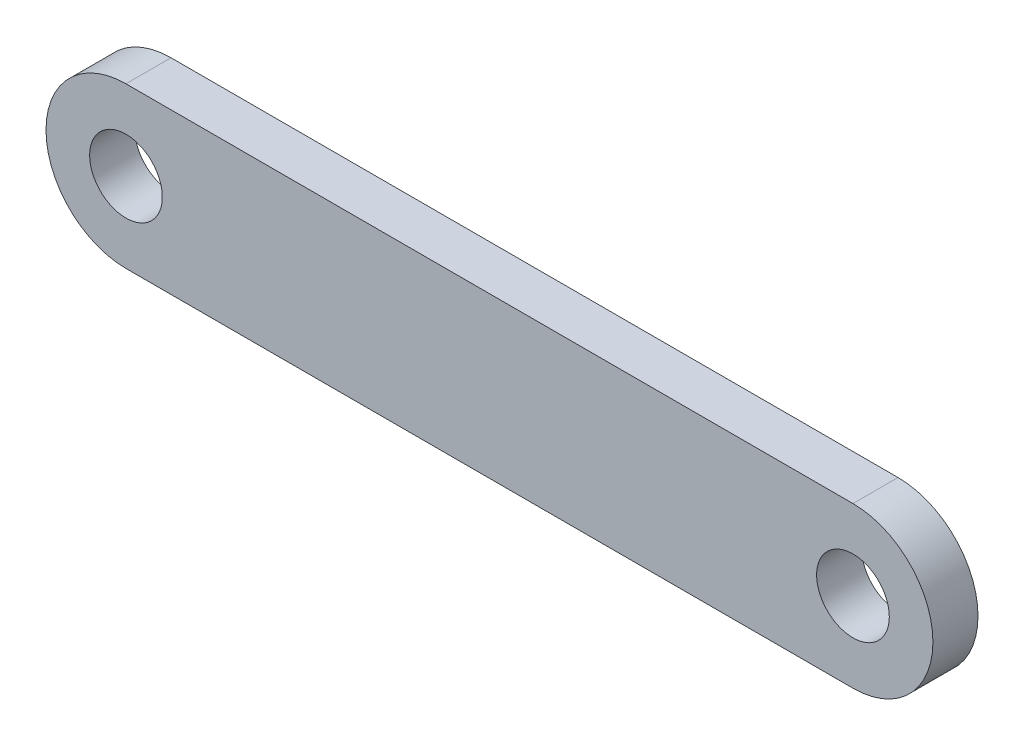
SolidWorks part; units mm, degrees
material "Teak"
ref_plane "Front Plane" through (0, 0, 0) normal (0, 0, 1) x (1, 0, 0)
ref_plane "Top Plane" through (0, 0, 0) normal (0, 1, 0) x (1, 0, 0)
ref_plane "Right Plane" through (0, 0, 0) normal (1, 0, 0) x (0, 0, -1)
sketch "Sketch1" plane through (0, 0, 0) normal (0, 0, 1) x (1, 0, 0)
  line L1 (0, 0) -> (0, 26.388) construction
  line L2 (-25, 5.0272) -> (25, 5.0272)
  line L3 (-25, -5.9728) -> (25, -5.9728)
  circle A0 centre (25, -0.4728) radius 2.5
  arc A1 (25, 5.0272) -> (25, -5.9728) centre (25, -0.4728) cw
  arc A2 (-25, 5.0272) -> (-25, -5.9728) centre (-25, -0.4728) ccw
  circle A3 centre (-25, -0.4728) radius 2.5
  point P8 (0, 5.0272)
  point P15 (0, -5.9728)
  dimension "D1" = 5
  dimension "D3" = 5.5
  dimension "D2" = 11
  dimension "D4" = 50
extrude "Boss-Extrude1" add sketch "Sketch1" along normal blind 3.1
equation "\"p\"= 20mm"
equation "\"m\"= 1"
equation "\"hole_diam\"= 4mm"
equation "\"len_grip_1\" = 50mm"
equation "\"len_grip_2\" = 50mm"
equation "\"thick\" = 3.1mm"
equation "\"thick2\" = 20mm"
equation "\"wrist_cont_bearing_diam\"=3in"
equation "\"wrist_cont_bearing_thick\"=5/16in"
equation "\"len_forearm\" = 300mm"
equation "\"wrist_bearing_diam\"=3in"
equation "\"len_link\" = 7cm"
equation "\"elbow_cont_bearing_diam\"=10cm"
equation "\"elbow_cont_bearing2_diam\"=7.5cm"
equation "\"small_bearing_outer\"=13mm"
equation "\"servo1_L\"=40.7mm"
equation "\"servo1_W\"=20.5mm"
equation "\"servo1_H\"=43.5mm"
equation "\"servo1_hL\"=49mm"
equation "\"servo1_hW\"=10mm"
equation "\"D3@Sketch1\"=\"D1@Sketch1\"/2 + 3"
equation "\"D4@Sketch1\"=\"len_grip_1\""
equation "\"D2@Sketch1\"=\"D3@Sketch1\"*2"
equation "\"servo1_H2\"=27mm"
equation "\"servo2_L\"=40.5mm"
equation "\"servo2_W\"=20mm"
equation "\"servo2_hL\"=49mm"
equation "\"servo2_hW\"=10mm"
equation "\"large_bearing_inner\"=2.75in"
equation "\"large_bearing_outer\"=4.75in"
equation "\"large_bearing_thick\"=3/8in"
equation "\"large_bearing_h1\"=3.25in"
equation "\"D1@Boss-Extrude1\"=\"thick\""
